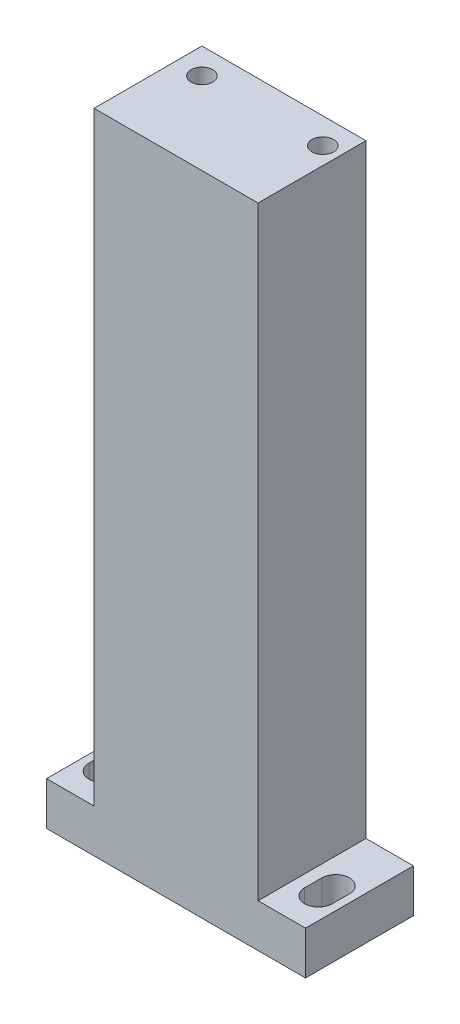
SolidWorks part; units mm, degrees
material "Plástico personalizado"
ref_plane "Plano frontal" through (0, 0, 0) normal (0, 0, 1) x (1, 0, 0)
ref_plane "Plano superior" through (0, 0, 0) normal (0, 1, 0) x (1, 0, 0)
ref_plane "Plano direito" through (0, 0, 0) normal (1, 0, 0) x (0, 0, -1)
sketch "Esboço1" plane through (0, 0, 0) normal (0, 1, 0) x (1, 0, 0)
  line L1 (-30, 12.5) -> (30, 12.5)
  line L2 (-30, 12.5) -> (-30, -12.5)
  line L3 (-30, -12.5) -> (30, -12.5)
  line L4 (30, 12.5) -> (30, -12.5)
  line L5 (-30, 12.5) -> (30, -12.5) construction
  line L6 (-30, -12.5) -> (30, 12.5) construction
  point P0 (0, 0)
  dimension "D1" = 60
  dimension "D2" = 25
extrude "Ressalto-extrusão1" add sketch "Esboço1" along normal blind 10
sketch "Esboço7" plane through (0, 10, 0) normal (0, 1, 0) x (1, 0, 0)
  line L0 (-30, -12.5) -> (30, -12.5) construction
  line L1 (-19, 12.5) -> (19, 12.5)
  line L2 (-19, 12.5) -> (-19, -12.5)
  line L3 (-19, -12.5) -> (19, -12.5)
  line L4 (19, 12.5) -> (19, -12.5)
  line L5 (-19, 12.5) -> (19, -12.5) construction
  line L6 (-19, -12.5) -> (19, 12.5) construction
  point P0 (0, 0)
  dimension "D1" = 38
extrude "Ressalto-extrusão3" add sketch "Esboço7" along normal blind 140
sketch "Esboço8" plane through (0, 150, 0) normal (0, 1, 0) x (1, 0, 0)
  line L0 (-19, 12.5) -> (-19, -12.5) construction
  line L1 (19, 12.5) -> (-19, 12.5) construction
  circle A0 centre (-13, 6.5) radius 2.5
  circle A1 centre (15, 6.5) radius 2.5
  dimension "D1" = 28
  dimension "D2" = 6
  dimension "D3" = 5
  dimension "D4" = 6
  dimension "D5" = 6
extrude "Corte-extrusão4" cut sketch "Esboço8" against normal blind 20
sketch "Esboço9" plane through (0, 10, 0) normal (0, 1, 0) x (1, 0, 0)
  line L0 (-25, -4.5) -> (-25, -0.5) construction
  line L1 (-28.2, -4.5) -> (-28.2, -0.5)
  line L2 (-21.8, -4.5) -> (-21.8, -0.5)
  line L3 (-30, 12.5) -> (-30, -12.5) construction
  line L4 (25, -4.5) -> (25, -0.5) construction
  line L5 (21.8, -4.5) -> (21.8, -0.5)
  line L6 (28.2, -4.5) -> (28.2, -0.5)
  line L7 (30, -12.5) -> (30, 12.5) construction
  line L8 (30, 12.5) -> (19, 12.5) construction
  line L9 (-19, 12.5) -> (-30, 12.5) construction
  arc A0 (-28.2, -4.5) -> (-21.8, -4.5) centre (-25, -4.5) ccw
  arc A1 (-21.8, -0.5) -> (-28.2, -0.5) centre (-25, -0.5) ccw
  arc A2 (21.8, -4.5) -> (28.2, -4.5) centre (25, -4.5) ccw
  arc A3 (28.2, -0.5) -> (21.8, -0.5) centre (25, -0.5) ccw
  point P2 (-25, -2.5)
  point P7 (-21.8, -2.5)
  point P12 (25, -2.5)
  dimension "D6" = 3.2
  dimension "D7" = 15
  dimension "D1" = 6.4
  dimension "D2" = 5
  dimension "D3" = 4
  dimension "D4" = 5
  dimension "D5" = 4
  dimension "D8" = 15
extrude "Corte-extrusão5" cut sketch "Esboço9" against normal blind 20
